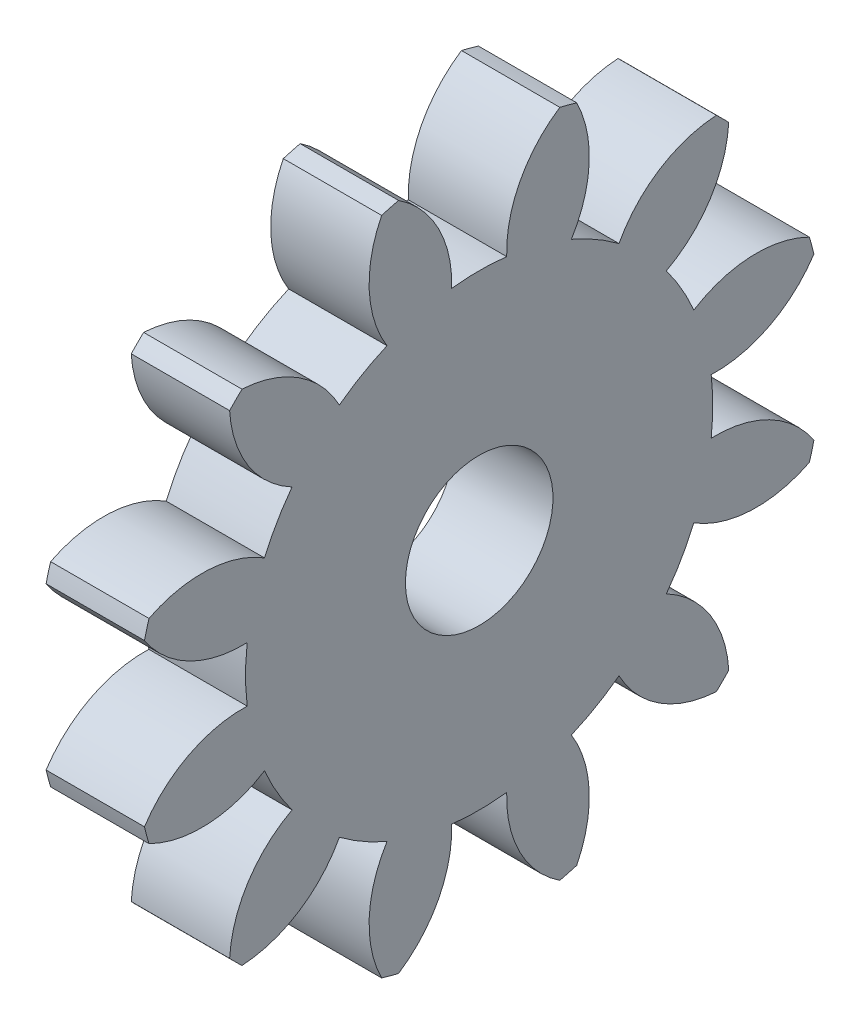
SolidWorks part; units mm, degrees
ref_plane "Plane1" through (0, 0, 0) normal (0, 0, 1) x (1, 0, 0)
ref_plane "Plane2" through (0, 0, 0) normal (0, 1, 0) x (1, 0, 0)
ref_plane "Plane3" through (0, 0, 0) normal (1, 0, 0) x (0, 0, -1)
sketch "HoldingSke" plane through (0, 0, 0) normal (0, 1, 0) x (1, 0, 0)
  line L0 (0, 0) -> (0.1534, -0.0354)
  line L1 (-15, 0) -> (100, 0) construction
  line L2 (0, 0) -> (-2.1039, 2.3779)
  line L3 (0, 0) -> (-11.863, 4.5341)
  line L4 (0, 0) -> (8.4473, 1.7955)
  line L5 (0, 0) -> (-23.7986, -8.8762)
  line L6 (0, 0) -> (-10.5278, -7.1032)
  line L7 (-2.1039, 2.3779) -> (3.3635, 27.1825)
  line L8 (-76.2, 54.61) -> (-73.66, 54.61)
  line L9 (-71.009, 38.7566) -> (-53.1078, 45.2721)
  line L10 (-76.2, 71.12) -> (104.1128, 71.12)
  line L11 (0, 0) -> (-12.7, 0)
  line L12 (-76.2, 101.6) -> (-75.9714, 101.6)
  line L13 (24.9733, 27.94) -> (52.9518, 28.4284)
  line L14 (24.9733, 27.94) -> (24.9746, 27.94)
  line L15 (24.9733, 27.94) -> (100.4006, 29.5858)
  line L16 (-63.627, -6.35) -> (-12.827, -6.35)
  circle A0 centre (0, 0) radius 9.525
  circle A1 centre (0, 0) radius 12.7
  circle A2 centre (0, 0) radius 12.7
  circle A3 centre (0, 0) radius 9.525
  dimension "MHD" = 25.4
  dimension "Hub_dia" = 25.4
  dimension "Bore" = 19.05
  dimension "MBD" = 19.05
  dimension "Num_teeth" = 12
  dimension "Pitch_radius" = 180.3128
  dimension "Pitch" = 0.1575
  dimension "Width" = 12.7
  dimension "Overall_len" = 25.4
  dimension "Show_teeth" = 13
  dimension "Thickness" = 12.7
  dimension "OAL" = 25.4001
  dimension "T_dim" = 2.54
  dimension "Ap" = 20
  dimension "H" = 19.05
  dimension "Backlash" = 0.2286
  dimension "Addendum_fac" = 1
  dimension "Dedendum_fac" = 1.25
  dimension "Clearance_fac" = 0.25
  dimension "Dedendum_add" = 0.0013
  dimension "Module" = 6.35
sketch "BasProSke" plane through (0, 0, 0) normal (0, 1, 0) x (1, 0, 0)
  line L0 (-10, 0) -> (60, 0) construction
  line L1 (0, 0) -> (0, 44.45)
  line L2 (0, 0) -> (12.7, 0)
  line L3 (12.7, 0) -> (12.7, 44.45)
  line L4 (12.7, 44.45) -> (0, 44.45)
  dimension "Diameter" = 88.9
  dimension "Thickness" = 12.7
revolve "Base-Revolve" add sketch "BasProSke" angle 360 about L0
sketch "TooCutSke" plane through (0, 0, 0) normal (1, 0, 0) x (0, 0, -1)
  line L1 (0, 0) -> (0, 107) construction
  line L2 (0, 0) -> (-5.3725, 37.7193) construction
  line L3 (0, 0) -> (-19.5794, 73.0714) construction
  line L4 (-5.3725, 37.7193) -> (-9.7897, 36.5357) construction
  arc A0 (3.5522, 29.9513) -> (-3.5522, 29.9513) centre (0, 0) ccw
  arc A1 (10.4397, 43.2328) -> (-10.4397, 43.2328) centre (0, 0) ccw
  circle A2 centre (0, 0) radius 38.1 construction
  circle A3 centre (0, 0) radius 35.8023 construction
  arc A4 (-3.5522, 29.9513) -> (-10.4397, 43.2328) centre (-18.7831, 30.4795) ccw
  arc A5 (10.4397, 43.2328) -> (3.5522, 29.9513) centre (18.7831, 30.4795) ccw
  dimension "Root_dia" = 60.3225
  dimension "Overcut_dia" = 88.9508
  dimension "Pitch_dia" = 76.2
  dimension "Base_dia" = 71.6046
  dimension "Flank_rad" = 15.24
  dimension "Half_ang" = 15
  dimension "Half_CT" = 4.573
extrude "ToothCut" cut sketch "TooCutSke" along normal through all
fillet "Breaks" [suppressed] radius 0.127
fillet "RootFillets" [suppressed] radius 1.5888
pattern_circular "TeethCuts" count 12 every 30 about axis through (-10, 0, 0) along (1, 0, 0) of "ToothCut", "RootFillets", "Breaks"
sketch "HubNeaOneSke" plane through (0, 0, 0) normal (-1, 0, 0) x (0, 0, 1)
  circle A0 centre (0, 0) radius 12.7
  dimension "Diameter" = 25.4
extrude "HubNearOne" [suppressed] add sketch "HubNeaOneSke" along normal blind 12.7001
sketch "HubNeaBotSke" plane through (0, 0, 0) normal (-1, 0, 0) x (0, 0, 1)
  circle A0 centre (0, 0) radius 12.7
  dimension "Diameter" = 25.4
extrude "HubNearBoth" [suppressed] add sketch "HubNeaBotSke" along normal blind 6.35
ref_plane "FarPln" through (12.7, 0, 0) normal (1, 0, 0) x (0, 0, -1)
sketch "HubFarSke" plane through (12.7, 0, 0) normal (1, 0, 0) x (0, 0, -1)
  circle A0 centre (0, 0) radius 12.7
  dimension "Diameter" = 25.4
extrude "HubFar" [suppressed] add sketch "HubFarSke" along normal blind 6.35
sketch "BorSke" plane through (0, 0, 0) normal (1, 0, 0) x (0, 0, -1)
  circle A0 centre (0, 0) radius 9.525
  dimension "Diameter" = 19.05
extrude "Bore" cut sketch "BorSke" along normal mid plane 50.8001
sketch "KeySke" plane through (0, 0, 0) normal (1, 0, 0) x (0, 0, -1)
  line L0 (-3.175, 0) -> (-3.175, 12.065)
  line L1 (-3.175, 12.065) -> (3.175, 12.065)
  line L2 (3.175, 12.065) -> (3.175, 0)
  line L3 (0, 0) -> (0, 34) construction
  line L4 (-3.175, 0) -> (3.175, 0)
  dimension "Offset" = 12.065
  dimension "Width" = 6.35
extrude "Keyway" [suppressed] cut sketch "KeySke" along normal mid plane 50.8001
pattern_circular "Keyway2" [suppressed] count 2 every 90 about axis through (-10, 0, 0) along (1, 0, 0)
equation "' \"Module@HoldingSke\" = 6.35"
equation "' \"Num_teeth@HoldingSke\" = 12"
equation "' \"Ap@HoldingSke\" =  20"
equation "' \"Width@HoldingSke\" = 0.5 * 25.4"
equation "' \"Hub_dia@HoldingSke\"= 1 * 25.4"
equation "' \"Overall_len@HoldingSke\" = 1.0 * 25.4"
equation "' \"Bore@HoldingSke\" = 0.75 * 25.4"
equation "' \"T_dim@HoldingSke\" = 0.1 * 25.4"
equation "' \"Width@KeySke\" = 0.25 * 25.4"
equation "' \"Show_teeth@HoldingSke\" = 13"
equation "' \"Backlash@HoldingSke\" = 0.009 * 25.4"
equation "' \"Addendum_fac@HoldingSke\" = 1.0"
equation "' \"Dedendum_fac@HoldingSke\" = 1.25"
equation "' \"Dedendum_add@HoldingSke\" = 0.00005 * 25.4"
equation "' \"Clearance_fac@HoldingSke\" = 0.25"
equation "\"Pitch@HoldingSke\" = 1 / \"Module@HoldingSke\""
equation "\"Overcut_dia@TooCutSke\" = (\"Num_teeth@HoldingSke\" + 2 * \"Addendum_fac@HoldingSke\") / \"Pitch@HoldingSke\" + 0.002 * 25.4"
equation "\"Pitch_dia@TooCutSke\" = \"Num_teeth@HoldingSke\" / \"Pitch@HoldingSke\""
equation "\"Base_dia@TooCutSke\" = \"Num_teeth@HoldingSke\" / \"Pitch@HoldingSke\" * cos((\"Ap@HoldingSke\"  * 3.14159265 / 180))"
equation "\"Root_dia@TooCutSke\" = (\"Num_teeth@HoldingSke\" + 2) / \"Pitch@HoldingSke\" - 2 * (\"Addendum_fac@HoldingSke\" + \"Dedendum_fac@HoldingSke\") / \"Pitch@HoldingSke\" - \"Dedendum_add@HoldingSke\" * 2"
equation "\"Half_ang@TooCutSke\" = 180 / \"Num_teeth@HoldingSke\""
equation "\"Half_CT@TooCutSke\" = \"Num_teeth@HoldingSke\" / \"Pitch@HoldingSke\" * sin((3.14159265 / 2 / \"Num_teeth@HoldingSke\")) / 2 - 7 * \"Backlash@HoldingSke\" / 4"
equation "\"Flank_rad@TooCutSke\" = \"Num_teeth@HoldingSke\" / \"Pitch@HoldingSke\" / 5"
equation "\"Radius@RootFillets\" = \"Clearance_fac@HoldingSke\" / \"Pitch@HoldingSke\" + \"Dedendum_add@HoldingSke\""
equation "\"Break_rad@Breaks\" = 0.02 / \"Pitch@HoldingSke\""
equation "\"Thickness@HoldingSke\" = \"Width@HoldingSke\""
equation "\"OAL@HoldingSke\" = \"Thickness@HoldingSke\""
equation "\"MHD@HoldingSke\" = (\"Num_teeth@HoldingSke\" + 2) / \"Pitch@HoldingSke\" - 2 * (\"Addendum_fac@HoldingSke\" + \"Dedendum_fac@HoldingSke\")  / \"Pitch@HoldingSke\" - \"Dedendum_add@HoldingSke\" * 2"
equation "\"MBD@HoldingSke\" = (\"Num_teeth@HoldingSke\" + 2) / \"Pitch@HoldingSke\" - 2 * (\"Addendum_fac@HoldingSke\" + \"Dedendum_fac@HoldingSke\")  / \"Pitch@HoldingSke\" - \"Dedendum_add@HoldingSke\" * 2 - 0.002 * 25.4"
equation "\"MHD@HoldingSke\" = ((sgn( \"MHD@HoldingSke\" - \"Hub_dia@HoldingSke\" )-1)*( \"MHD@HoldingSke\" - \"Hub_dia@HoldingSke\" ))/-2+ \"Hub_dia@HoldingSke\""
equation "\"MBD@HoldingSke\" = ((sgn( \"MBD@HoldingSke\" - \"Bore@HoldingSke\" )-1)*( \"MBD@HoldingSke\" - \"Bore@HoldingSke\" ))/-2+ \"Bore@HoldingSke\""
equation "\"OAL@HoldingSke\" = ((sgn( \"OAL@HoldingSke\" - \"Overall_len@HoldingSke\" )+1)*( \"OAL@HoldingSke\" - \"Overall_len@HoldingSke\" ))/2 + \"Overall_len@HoldingSke\" + 0.000002 * 25.4"
equation "\"Num_teeth@TeethCuts\" = int( \"Show_teeth@HoldingSke\" ) + 1"
equation "\"Num_teeth@TeethCuts\" = ((sgn( \"Num_teeth@TeethCuts\" - \"Num_teeth@HoldingSke\" )-1)*( \"Num_teeth@TeethCuts\" - \"Num_teeth@HoldingSke\" ))/-2+ \"Num_teeth@HoldingSke\""
equation "\"Num_teeth@TeethCuts\" = ((sgn( \"Num_teeth@TeethCuts\" - 2.0)+1)*( \"Num_teeth@TeethCuts\" - 2.0))/2 +2.0"
equation "\"Angle@TeethCuts\" = 360.0 / \"Num_teeth@HoldingSke\""
equation "\"Diameter@BasProSke\" = (\"Num_teeth@HoldingSke\" + 2 * \"Addendum_fac@HoldingSke\") / \"Pitch@HoldingSke\""
equation "\"Thickness@BasProSke\"  = \"Thickness@HoldingSke\""
equation "' \"Fillet_rad@BasProSke\" =  \"Thickness@HoldingSke\" * 0.05"
equation "\"MHD@HoldingSke\" = ((sgn( \"MHD@HoldingSke\" - \"Root_dia@TooCutSke\" )-1)*( \"MHD@HoldingSke\" - \"Root_dia@TooCutSke\" ))/-2+ \"Root_dia@TooCutSke\""
equation "\"Diameter@HubNeaOneSke\" = \"MHD@HoldingSke\""
equation "\"Length@HubNearOne\" = \"OAL@HoldingSke\" - \"Thickness@BasProSke\""
equation "\"Diameter@HubNeaBotSke\" = \"MHD@HoldingSke\""
equation "\"Length@HubNearBoth\" = ( \"OAL@HoldingSke\" - \"Thickness@BasProSke\" ) / 2.0"
equation "\"Thickness@FarPln\" = \"Thickness@BasProSke\""
equation "\"Diameter@HubFarSke\" = \"MHD@HoldingSke\""
equation "\"Length@HubFar\" = ( \"OAL@HoldingSke\" - \"Thickness@BasProSke\" ) / 2.0"
equation "\"Diameter@BorSke\" = \"MBD@HoldingSke\""
equation "\"D1@Bore\" = \"OAL@HoldingSke\" * 2.0"
equation "\"D1@Keyway\" = \"OAL@HoldingSke\" * 2.0"
equation "\"Offset@KeySke\" = \"T_dim@HoldingSke\" + \"MBD@HoldingSke\" / 2.0"
